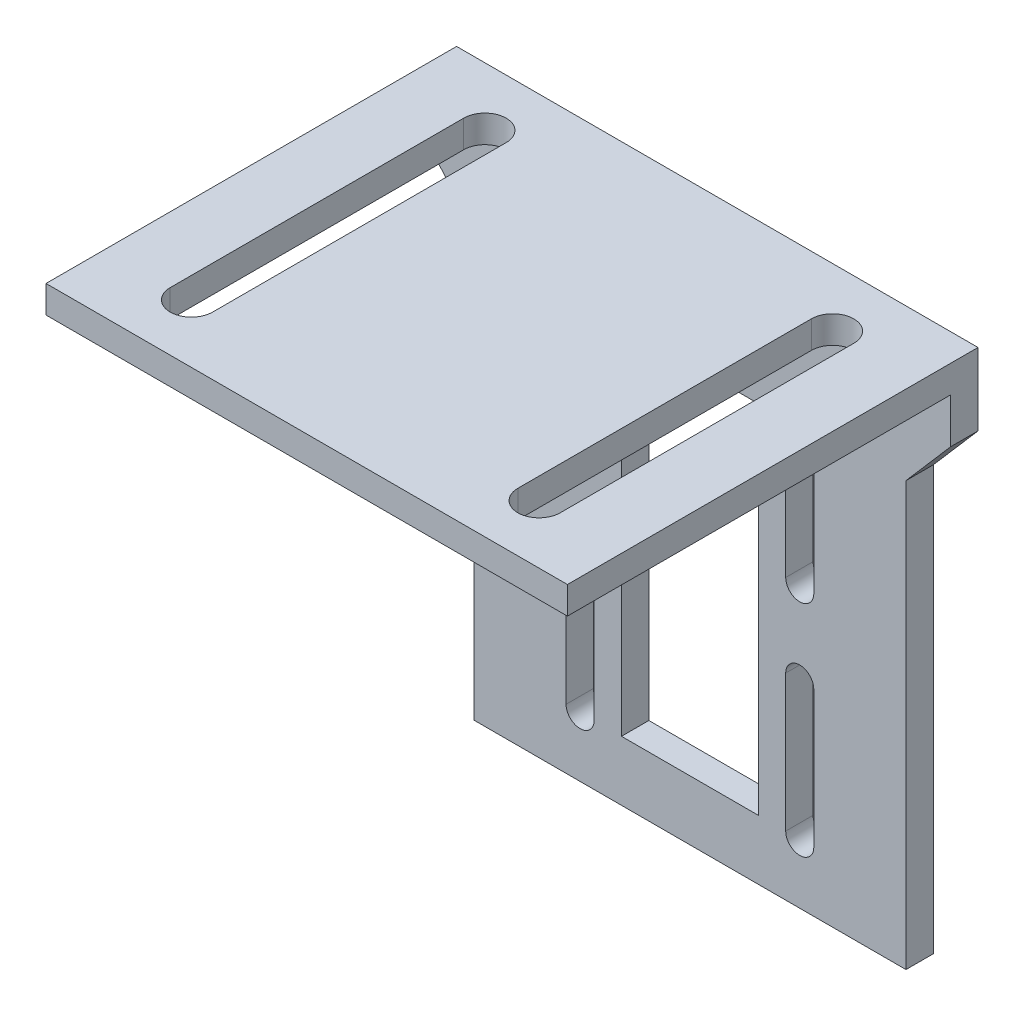
SolidWorks part; units mm, degrees
ref_plane "Front Plane" through (0, 0, 0) normal (0, 0, 1) x (1, 0, 0)
ref_plane "Top Plane" through (0, 0, 0) normal (0, 1, 0) x (1, 0, 0)
ref_plane "Right Plane" through (0, 0, 0) normal (1, 0, 0) x (0, 0, -1)
sketch "Sketch1" plane through (0, 0, 0) normal (1, 0, 0) x (0, 0, -1)
  line L1 (0, 0) -> (-2, 0)
  line L2 (0, 0) -> (0, 40)
  line L3 (0, 40) -> (-30, 40)
  line L4 (-30, 38) -> (-30, 40)
  line L7 (-30, 38) -> (-2, 38)
  line L8 (-2, 0) -> (-2, 38)
  dimension "D1" = 40
  dimension "D2" = 30
  dimension "D3" = 2
extrude "Boss-Extrude1" add sketch "Sketch1" along normal mid plane 38.1
sketch "Sketch2" plane through (0, 40, 0) normal (0, 1, 0) x (1, 0, 0)
  line L0 (12.7, -25.7242) -> (12.7, -4.2758) construction
  line L1 (11.15, -25.7242) -> (11.15, -4.2758)
  line L2 (14.25, -25.7242) -> (14.25, -4.2758)
  line L3 (0, 0) -> (0, -30) construction
  line L4 (19.05, 0) -> (-19.05, 0) construction
  line L5 (19.05, -30) -> (-19.05, -30) construction
  line L6 (-12.7, -25.7242) -> (-12.7, -4.2758) construction
  line L7 (-11.15, -25.7242) -> (-11.15, -4.2758)
  line L8 (-14.25, -25.7242) -> (-14.25, -4.2758)
  line L9 (12.7, -25.7242) -> (12.7, -30) construction
  line L10 (12.7, -4.2758) -> (12.7, 0) construction
  arc A0 (11.15, -25.7242) -> (14.25, -25.7242) centre (12.7, -25.7242) ccw
  arc A1 (14.25, -4.2758) -> (11.15, -4.2758) centre (12.7, -4.2758) ccw
  arc A2 (-11.15, -25.7242) -> (-14.25, -25.7242) centre (-12.7, -25.7242) cw
  arc A3 (-14.25, -4.2758) -> (-11.15, -4.2758) centre (-12.7, -4.2758) cw
  point P2 (12.7, -15)
  point P15 (-12.7, -15)
  point P22 (6.8044, -15)
  point P25 (6.7946, -25.7242)
  dimension "D1" = 12.7
  dimension "D2" = 3.1
extrude "Cut-Extrude1" cut sketch "Sketch2" against normal mid plane 38.1
sketch "Sketch3" plane through (0, 0, 2) normal (0, 0, 1) x (1, 0, 0)
  line L0 (-8.025, 30.4195) -> (-8.025, 20.4195) construction
  line L1 (-6.9987, 30.4195) -> (-6.9987, 20.4195)
  line L2 (-9.0513, 30.4195) -> (-9.0513, 20.4195)
  line L3 (-8.025, 14.3695) -> (-8.025, 4.3695) construction
  line L4 (-6.9987, 14.3695) -> (-6.9987, 4.3695)
  line L5 (-9.0513, 14.3695) -> (-9.0513, 4.3695)
  line L6 (0, 0) -> (0, 38) construction
  line L7 (19.05, 38) -> (-19.05, 38) construction
  line L8 (5, 30.4195) -> (5, 4.3695)
  line L9 (5, 30.4195) -> (-5, 30.4195)
  line L10 (0, 30.4195) -> (0, 4.3695)
  line L11 (5, 4.3695) -> (-5, 4.3695)
  line L12 (-5, 30.4195) -> (-5, 4.3695)
  line L13 (8.025, 14.3695) -> (8.025, 4.3695) construction
  line L14 (6.9987, 14.3695) -> (6.9987, 4.3695)
  line L15 (9.0513, 14.3695) -> (9.0513, 4.3695)
  line L16 (8.025, 30.4195) -> (8.025, 20.4195) construction
  line L17 (6.9987, 30.4195) -> (6.9987, 20.4195)
  line L18 (9.0513, 30.4195) -> (9.0513, 20.4195)
  line L19 (-19.05, 34.716) -> (-15.7864, 30.9424)
  line L20 (-19.05, 38) -> (-19.05, 0) construction
  line L21 (-15.7864, 30.9424) -> (-15.7864, 0)
  line L22 (19.05, 0) -> (-19.05, 0) construction
  line L23 (-19.05, 34.716) -> (-19.05, 0)
  line L24 (-19.05, 0) -> (-15.7864, 0)
  line L25 (19.05, 34.716) -> (19.05, 0)
  line L26 (19.05, 34.716) -> (15.7864, 30.9424)
  line L27 (15.7864, 30.9424) -> (15.7864, 0)
  line L28 (19.05, 0) -> (15.7864, 0)
  arc A0 (-6.9987, 30.4195) -> (-9.0513, 30.4195) centre (-8.025, 30.4195) ccw
  arc A1 (-9.0513, 20.4195) -> (-6.9987, 20.4195) centre (-8.025, 20.4195) ccw
  arc A2 (-6.9987, 14.3695) -> (-9.0513, 14.3695) centre (-8.025, 14.3695) ccw
  arc A3 (-9.0513, 4.3695) -> (-6.9987, 4.3695) centre (-8.025, 4.3695) ccw
  arc A4 (6.9987, 14.3695) -> (9.0513, 14.3695) centre (8.025, 14.3695) cw
  arc A5 (9.0513, 4.3695) -> (6.9987, 4.3695) centre (8.025, 4.3695) cw
  arc A6 (6.9987, 30.4195) -> (9.0513, 30.4195) centre (8.025, 30.4195) cw
  arc A7 (9.0513, 20.4195) -> (6.9987, 20.4195) centre (8.025, 20.4195) cw
  point P2 (-8.025, 25.4195)
  point P7 (-8.025, 9.3695)
  point P30 (8.025, 9.3695)
  point P37 (8.025, 25.4195)
  line M5 (-19.05, 38) -> (-19.05, 0)
  line M6 (-19.05, 0) -> (19.05, 0)
  line M7 (19.05, 0) -> (19.05, 38)
  dimension "D1" = 2.0526
  dimension "D2" = 16.05
  dimension "D3" = 10
  dimension "D4" = 8.025
  dimension "D5" = 5
extrude "Cut-Extrude2" cut sketch "Sketch3" against normal through all contours L11 L8 L9 L10 | L9 L12 L11 L10 | L2 A1 L1 A0 | L5 A3 L4 A2 | A7 L18 A6 L17 | A5 L15 A4 L14 | L21 L19 M5 M6 | L26 L27 M6 M7
